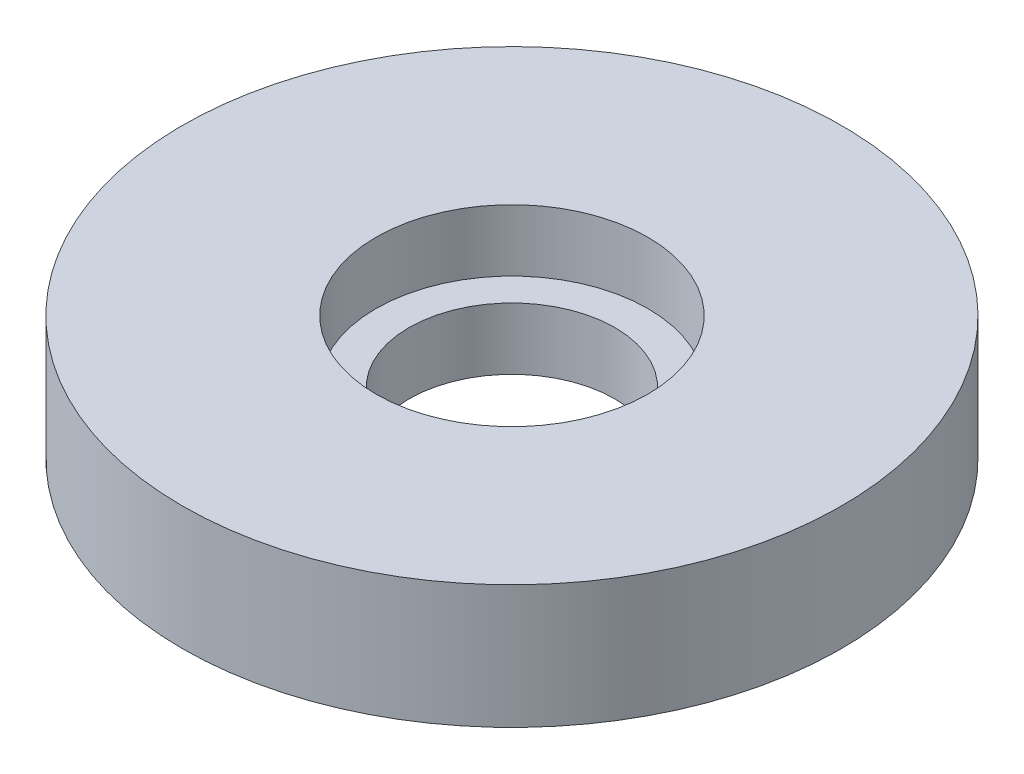
SolidWorks part; units mm, degrees
ref_plane "Front Plane" through (0, 0, 0) normal (0, 0, 1) x (1, 0, 0)
ref_plane "Top Plane" through (0, 0, 0) normal (0, 1, 0) x (1, 0, 0)
ref_plane "Right Plane" through (0, 0, 0) normal (1, 0, 0) x (0, 0, -1)
sketch "Sketch1" plane through (0, 0, 0) normal (0, 1, 0) x (1, 0, 0)
  circle A0 centre (0, 0) radius 16
extrude "Boss-Extrude1" add sketch "Sketch1" along normal blind 6
sketch "Sketch4" plane through (0, 6, 0) normal (0, 1, 0) x (1, 0, 0)
  circle A0 centre (0, 0) radius 6.6
extrude "Cut-Extrude2" cut sketch "Sketch4" against normal blind 3
sketch "Sketch5" plane through (0, 0, 0) normal (0, -1, 0) x (-1, 0, 0)
  circle A0 centre (0, 0) radius 5
extrude "Cut-Extrude3" cut sketch "Sketch5" against normal blind 3
